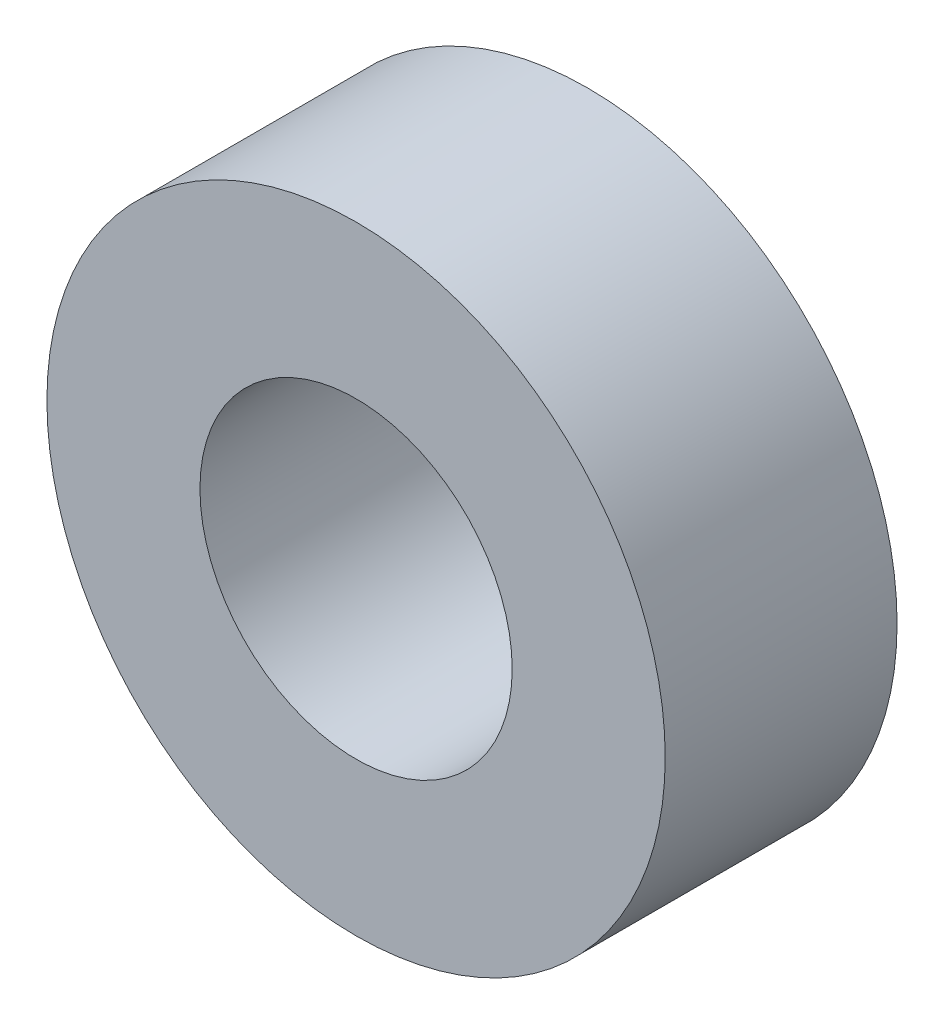
SolidWorks part; units mm, degrees
material "Water"
ref_plane "Front Plane" through (0, 0, 0) normal (0, 0, 1) x (1, 0, 0)
ref_plane "Top Plane" through (0, 0, 0) normal (0, 1, 0) x (1, 0, 0)
ref_plane "Right Plane" through (0, 0, 0) normal (1, 0, 0) x (0, 0, -1)
sketch "Sketch1" plane through (0, 0, 0) normal (0, 0, 1) x (1, 0, 0)
  circle A0 centre (0, 0) radius 12.7
  circle A1 centre (0, 0) radius 6.4135
  dimension "OD" = 25.4
  dimension "ID" = 12.827
extrude "Extrude1" add sketch "Sketch1" along normal mid plane 9.525
sketch "Sketch2" plane through (0, 0, 0) normal (1, 0, 0) x (0, 0, -1)
  line L0 (-4.7625, -6.4135) -> (4.7625, -6.4135) construction
  line L3 (4.7625, 6.4135) -> (-4.7625, 6.4135) construction
  line L5 (-4.7625, -6.4135) -> (4.7625, -6.4135)
  line L6 (4.7625, 6.4135) -> (-4.7625, 6.4135)
sketch "Sketch4" plane through (0, 0, 4.7625) normal (0, 0, 1) x (1, 0, 0)
  line L0 (0, 0) -> (-4.535, 4.535)
  line L1 (0, -2.1828) -> (0, 2.1828) construction
  circle A0 centre (0, 0) radius 6.4135 construction
  dimension "D1" = 45
